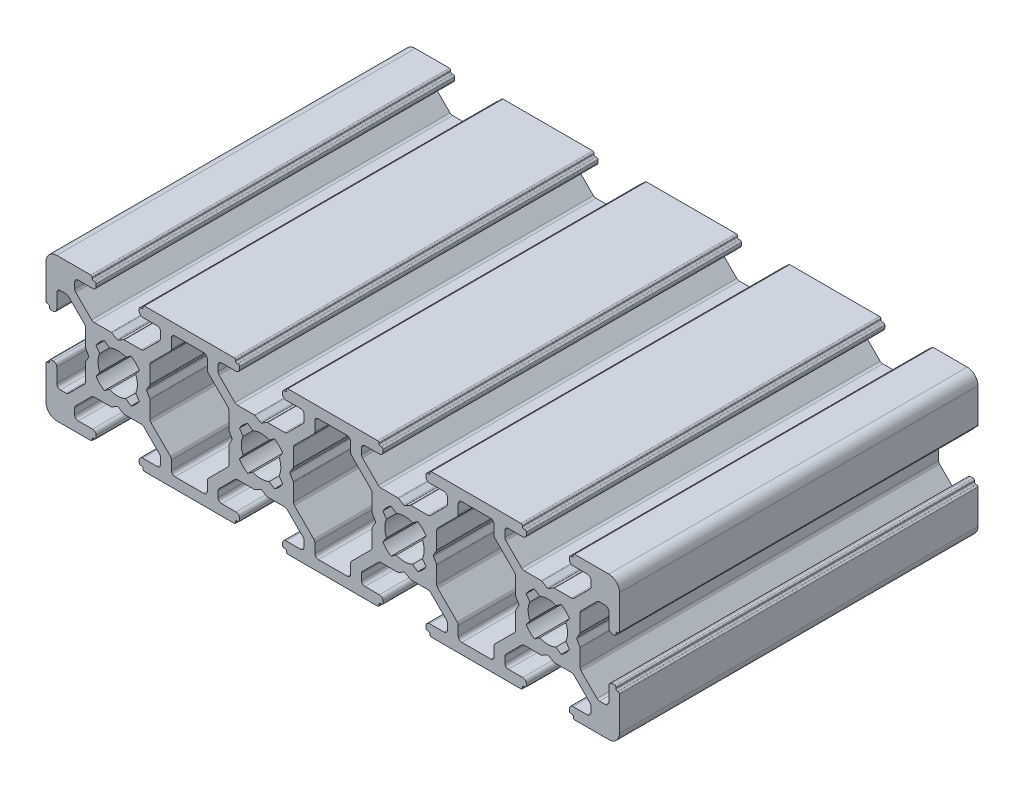
SolidWorks part; units mm, degrees
material "1060 СплавА"
ref_plane "Спереди" through (0, 0, 0) normal (0, 0, 1) x (1, 0, 0)
ref_plane "Сверху" through (0, 0, 0) normal (0, 1, 0) x (1, 0, 0)
ref_plane "Справа" through (0, 0, 0) normal (1, 0, 0) x (0, 0, -1)
sketch "Эскиз1" plane through (0, 0, 0) normal (0, 0, 1) x (1, 0, 0)
  line L0 (3.1454, -5.8536) -> (2.6464, -6.3525)
  line L1 (5.5, 0.9196) -> (5.5, 3.2919)
  line L2 (-13.6454, 4.6464) -> (-15.8536, 6.8546)
  line L3 (-18, 6) -> (-17.2081, 6)
  line L4 (-14.5, 0.9196) -> (-14.5, 3.2919)
  line L5 (-6.3546, -4.6464) -> (-4.1464, -6.8546)
  line L6 (-19.3, 3) -> (-19, 3)
  line L7 (-19.5, 3.35) -> (-19.5, 3.2)
  line L8 (-19.8, 3.55) -> (-19.7, 3.55)
  line L9 (-20, 8.5) -> (-20, 3.75)
  line L10 (-13.0204, 1.8653) -> (-12.5065, 1.1313)
  line L11 (-18.5, 3.5) -> (-18.5, 5.5)
  line L12 (-13.75, 10) -> (-18.5, 10)
  line L13 (-14.6464, 3.6454) -> (-16.8546, 5.8536)
  line L14 (-10.9196, 4.5) -> (-13.2919, 4.5)
  line L15 (-16, 8) -> (-16, 7.2081)
  line L16 (-14.0577, -0.1) -> (-14.4732, -0.8196)
  line L17 (-14.0577, 0.1) -> (-14.4732, 0.8196)
  line L18 (-11.8653, 3.0204) -> (-11.1313, 2.5065)
  line L19 (6.25, 10) -> (-6.25, 10)
  line L20 (-8.1347, 3.0204) -> (-8.8687, 2.5065)
  line L21 (-5.5, -0.9196) -> (-5.5, -3.2919)
  line L22 (-6.7081, 4.5) -> (-9.0804, 4.5)
  line L23 (-2.5, 8) -> (-2.5, 6.7061)
  line L24 (-3.1454, 5.8536) -> (-2.6464, 6.3525)
  line L25 (-10.1, 4.0577) -> (-10.8196, 4.4732)
  line L26 (-6.9796, 1.8653) -> (-7.4935, 1.1313)
  line L27 (-6.9796, -1.8653) -> (-7.4935, -1.1313)
  line L28 (-8.1347, -3.0204) -> (-8.8687, -2.5065)
  line L29 (-11.8653, -3.0204) -> (-11.1313, -2.5065)
  line L30 (-13.0204, -1.8653) -> (-12.5065, -1.1313)
  line L31 (-9.9, 4.0577) -> (-9.1804, 4.4732)
  line L32 (-13.5, 8.5) -> (-15.5, 8.5)
  line L33 (-13.55, 9.8) -> (-13.55, 9.7)
  line L34 (-13.35, 9.5) -> (-13.2, 9.5)
  line L35 (-13, 9.3) -> (-13, 9)
  line L36 (-10.9196, 4.5) -> (-13.2919, 4.5)
  line L37 (2, 8.5) -> (-2, 8.5)
  line L38 (-7, 9.3) -> (-7, 9)
  line L39 (-5.3536, 3.6454) -> (-3.1454, 5.8536)
  line L40 (-4, 8) -> (-4, 7.2081)
  line L41 (-6.3546, 4.6464) -> (-4.1464, 6.8546)
  line L42 (-6.65, 9.5) -> (-6.8, 9.5)
  line L43 (-6.45, 9.8) -> (-6.45, 9.7)
  line L44 (-6.5, 8.5) -> (-4.5, 8.5)
  line L45 (5.9423, -0.1) -> (5.5268, -0.8196)
  line L46 (-6.3546, -4.6464) -> (-4.1464, -6.8546)
  line L47 (-5.3536, -3.6454) -> (-3.1454, -5.8536)
  line L48 (-6.5, -8.5) -> (-4.5, -8.5)
  line L49 (-6.45, -9.8) -> (-6.45, -9.7)
  line L50 (-6.65, -9.5) -> (-6.8, -9.5)
  line L51 (-4, -8) -> (-4, -7.2081)
  line L52 (-5.3536, -3.6454) -> (-3.1454, -5.8536)
  line L53 (-7, -9.3) -> (-7, -9)
  line L54 (2, -8.5) -> (-2, -8.5)
  line L55 (-10.9196, -4.5) -> (-13.2919, -4.5)
  line L56 (-13, -9.3) -> (-13, -9)
  line L57 (-13.35, -9.5) -> (-13.2, -9.5)
  line L58 (-13.55, -9.8) -> (-13.55, -9.7)
  line L59 (-13.5, -8.5) -> (-15.5, -8.5)
  line L60 (-9.9, -4.0577) -> (-9.1804, -4.4732)
  line L61 (-13.0204, 1.8653) -> (-12.5065, 1.1313)
  line L62 (-11.8653, 3.0204) -> (-11.1313, 2.5065)
  line L63 (-8.1347, 3.0204) -> (-8.8687, 2.5065)
  line L64 (-6.9796, 1.8653) -> (-7.4935, 1.1313)
  line L65 (-6.9796, -1.8653) -> (-7.4935, -1.1313)
  line L66 (-10.1, -4.0577) -> (-10.8196, -4.4732)
  line L67 (-2.5, -8) -> (-2.5, -6.7061)
  line L68 (-6.7081, -4.5) -> (-9.0804, -4.5)
  line L69 (-5.9423, 0.1) -> (-5.5268, 0.8196)
  line L70 (-8.1347, -3.0204) -> (-8.8687, -2.5065)
  line L71 (-11.8653, -3.0204) -> (-11.1313, -2.5065)
  line L72 (-14.0577, -0.1) -> (-14.4732, -0.8196)
  line L73 (-14.0577, 0.1) -> (-14.4732, 0.8196)
  line L74 (-16, -8) -> (-16, -7.2081)
  line L75 (-10.9196, -4.5) -> (-13.2919, -4.5)
  line L76 (-14.6464, -3.6454) -> (-16.8546, -5.8536)
  line L77 (-13.75, -10) -> (-18.5, -10)
  line L78 (-18.5, -3.5) -> (-18.5, -5.5)
  line L79 (-13.0204, -1.8653) -> (-12.5065, -1.1313)
  line L80 (-20, -8.5) -> (-20, -3.75)
  line L81 (-19.8, -3.55) -> (-19.7, -3.55)
  line L82 (-19.5, -3.35) -> (-19.5, -3.2)
  line L83 (-19.3, -3) -> (-19, -3)
  line L84 (-14.5, -0.9196) -> (-14.5, -3.2919)
  line L85 (-18, -6) -> (-17.2081, -6)
  line L86 (-13.6454, -4.6464) -> (-15.8536, -6.8546)
  line L87 (6.25, -10) -> (-6.25, -10)
  line L88 (-5.3536, -3.6454) -> (-3.1454, -5.8536)
  line L89 (-5.9423, -0.1) -> (-5.5268, -0.8196)
  line L90 (-5.9423, 0.1) -> (-5.5268, 0.8196)
  line L91 (-5.9423, -0.1) -> (-5.5268, -0.8196)
  line L92 (-5.5, 0.9196) -> (-5.5, 3.2919)
  line L93 (-3.1454, -5.8536) -> (-2.6464, -6.3525)
  line L94 (5.9423, 0.1) -> (5.5268, 0.8196)
  line L95 (5.9423, -0.1) -> (5.5268, -0.8196)
  line L96 (5.3536, -3.6454) -> (3.1454, -5.8536)
  line L97 (13.6454, -4.6464) -> (15.8536, -6.8546)
  line L99 (14.5, -0.9196) -> (14.5, -3.2919)
  line L100 (13.75, 10) -> (26.25, 10)
  line L101 (13.75, -10) -> (26.25, -10)
  line L102 (13.6454, -4.6464) -> (15.8536, -6.8546)
  line L103 (14.5, -0.9196) -> (14.5, -3.2919)
  line L104 (13.0204, -1.8653) -> (12.5065, -1.1313)
  line L105 (17.5, 8) -> (17.5, 6.7061)
  line L106 (16.8546, 5.8536) -> (17.3536, 6.3525)
  line L107 (14.6464, -3.6454) -> (16.8546, -5.8536)
  line L108 (10.9196, -4.5) -> (13.2919, -4.5)
  line L109 (13.0204, 1.8653) -> (12.5065, 1.1313)
  line L110 (14.0577, 0.1) -> (14.4732, 0.8196)
  line L111 (14.0577, -0.1) -> (14.4732, -0.8196)
  line L112 (11.8653, -3.0204) -> (11.1313, -2.5065)
  line L113 (8.1347, -3.0204) -> (8.8687, -2.5065)
  line L114 (5.9423, 0.1) -> (5.5268, 0.8196)
  line L115 (6.7081, -4.5) -> (9.0804, -4.5)
  line L116 (2.5, -8) -> (2.5, -6.7061)
  line L117 (10.1, -4.0577) -> (10.8196, -4.4732)
  line L118 (6.9796, -1.8653) -> (7.4935, -1.1313)
  line L119 (6.9796, 1.8653) -> (7.4935, 1.1313)
  line L120 (8.1347, 3.0204) -> (8.8687, 2.5065)
  line L121 (11.8653, 3.0204) -> (11.1313, 2.5065)
  line L122 (13.0204, 1.8653) -> (12.5065, 1.1313)
  line L123 (9.9, -4.0577) -> (9.1804, -4.4732)
  line L124 (13.0204, -1.8653) -> (12.5065, -1.1313)
  line L125 (13, 9.3) -> (13, 9)
  line L126 (14.6464, 3.6454) -> (16.8546, 5.8536)
  line L127 (16, 8) -> (16, 7.2081)
  line L128 (10.9196, -4.5) -> (13.2919, -4.5)
  line L129 (7, -9.3) -> (7, -9)
  line L130 (5.3536, -3.6454) -> (3.1454, -5.8536)
  line L131 (4, -8) -> (4, -7.2081)
  line L132 (6.65, -9.5) -> (6.8, -9.5)
  line L133 (6.45, -9.8) -> (6.45, -9.7)
  line L134 (6.5, -8.5) -> (4.5, -8.5)
  line L135 (5.3536, -3.6454) -> (3.1454, -5.8536)
  line L136 (6.3546, -4.6464) -> (4.1464, -6.8546)
  line L137 (6.5, 8.5) -> (4.5, 8.5)
  line L138 (6.45, 9.8) -> (6.45, 9.7)
  line L139 (6.65, 9.5) -> (6.8, 9.5)
  line L140 (6.3546, 4.6464) -> (4.1464, 6.8546)
  line L141 (4, 8) -> (4, 7.2081)
  line L142 (5.3536, 3.6454) -> (3.1454, 5.8536)
  line L143 (7, 9.3) -> (7, 9)
  line L144 (10.9196, 4.5) -> (13.2919, 4.5)
  line L145 (13.6454, 4.6464) -> (15.8536, 6.8546)
  line L146 (13.35, 9.5) -> (13.2, 9.5)
  line L147 (13.55, 9.8) -> (13.55, 9.7)
  line L148 (13.5, 8.5) -> (15.5, 8.5)
  line L149 (9.9, 4.0577) -> (9.1804, 4.4732)
  line L150 (13.0204, -1.8653) -> (12.5065, -1.1313)
  line L151 (11.8653, -3.0204) -> (11.1313, -2.5065)
  line L152 (8.1347, -3.0204) -> (8.8687, -2.5065)
  line L153 (6.9796, -1.8653) -> (7.4935, -1.1313)
  line L154 (6.9796, 1.8653) -> (7.4935, 1.1313)
  line L155 (10.1, 4.0577) -> (10.8196, 4.4732)
  line L156 (3.1454, 5.8536) -> (2.6464, 6.3525)
  line L157 (2.5, 8) -> (2.5, 6.7061)
  line L158 (6.7081, 4.5) -> (9.0804, 4.5)
  line L159 (5.5, -0.9196) -> (5.5, -3.2919)
  line L160 (8.1347, 3.0204) -> (8.8687, 2.5065)
  line L161 (11.8653, 3.0204) -> (11.1313, 2.5065)
  line L162 (14.0577, 0.1) -> (14.4732, 0.8196)
  line L163 (14.0577, -0.1) -> (14.4732, -0.8196)
  line L164 (13.6454, -4.6464) -> (15.8536, -6.8546)
  line L165 (10.9196, 4.5) -> (13.2919, 4.5)
  line L166 (14.6464, 3.6454) -> (16.8546, 5.8536)
  line L167 (14.6464, -3.6454) -> (16.8546, -5.8536)
  line L168 (13.5, -8.5) -> (15.5, -8.5)
  line L169 (13.0204, 1.8653) -> (12.5065, 1.1313)
  line L170 (13.55, -9.8) -> (13.55, -9.7)
  line L171 (13.35, -9.5) -> (13.2, -9.5)
  line L172 (16, -8) -> (16, -7.2081)
  line L173 (14.6464, -3.6454) -> (16.8546, -5.8536)
  line L174 (6.3546, -4.6464) -> (4.1464, -6.8546)
  line L175 (14.5, 0.9196) -> (14.5, 3.2919)
  line L176 (13, -9.3) -> (13, -9)
  line L177 (13.6454, 4.6464) -> (15.8536, 6.8546)
  line L178 (13.0204, 1.8653) -> (12.5065, 1.1313)
  line L179 (13.0204, -1.8653) -> (12.5065, -1.1313)
  line L180 (17.5, -8) -> (17.5, -6.7061)
  line L181 (14.0577, 0.1) -> (14.4732, 0.8196)
  line L182 (14.6464, -3.6454) -> (16.8546, -5.8536)
  line L183 (14.0577, -0.1) -> (14.4732, -0.8196)
  line L184 (14.0577, 0.1) -> (14.4732, 0.8196)
  line L185 (18, -8.5) -> (22, -8.5)
  line L186 (14.0577, -0.1) -> (14.4732, -0.8196)
  line L187 (18, 8.5) -> (22, 8.5)
  line L188 (14.5, 0.9196) -> (14.5, 3.2919)
  line L189 (16.8546, -5.8536) -> (17.3536, -6.3525)
  line L190 (23.1454, -5.8536) -> (22.6464, -6.3525)
  line L191 (25.5, 0.9196) -> (25.5, 3.2919)
  line L192 (25.9423, -0.1) -> (25.5268, -0.8196)
  line L193 (25.9423, 0.1) -> (25.5268, 0.8196)
  line L194 (25.9423, -0.1) -> (25.5268, -0.8196)
  line L195 (25.3536, -3.6454) -> (23.1454, -5.8536)
  line L196 (25.9423, 0.1) -> (25.5268, 0.8196)
  line L197 (22.5, -8) -> (22.5, -6.7061)
  line L198 (26.9796, -1.8653) -> (27.4935, -1.1313)
  line L199 (26.9796, 1.8653) -> (27.4935, 1.1313)
  line L200 (26.3546, 4.6464) -> (24.1464, 6.8546)
  line L201 (27, -9.3) -> (27, -9)
  line L202 (25.5, 0.9196) -> (25.5, 3.2919)
  line L203 (33.6454, -4.6464) -> (35.8536, -6.8546)
  line L204 (25.3536, -3.6454) -> (23.1454, -5.8536)
  line L205 (24, -8) -> (24, -7.2081)
  line L206 (26.65, -9.5) -> (26.8, -9.5)
  line L207 (26.45, -9.8) -> (26.45, -9.7)
  line L208 (26.9796, 1.8653) -> (27.4935, 1.1313)
  line L209 (26.5, -8.5) -> (24.5, -8.5)
  line L210 (25.3536, -3.6454) -> (23.1454, -5.8536)
  line L211 (25.3536, 3.6454) -> (23.1454, 5.8536)
  line L212 (29.0804, 4.5) -> (26.7081, 4.5)
  line L213 (26.3546, -4.6464) -> (24.1464, -6.8546)
  line L214 (25.9423, -0.1) -> (25.5268, -0.8196)
  line L215 (25.9423, 0.1) -> (25.5268, 0.8196)
  line L216 (28.1347, 3.0204) -> (28.8687, 2.5065)
  line L217 (31.8653, 3.0204) -> (31.1313, 2.5065)
  line L218 (34.5, -0.9196) -> (34.5, -3.2919)
  line L219 (33.2919, 4.5) -> (30.9196, 4.5)
  line L220 (37.5, 8) -> (37.5, 6.7061)
  line L221 (36.8546, 5.8536) -> (37.3536, 6.3525)
  line L222 (29.9, 4.0577) -> (29.1804, 4.4732)
  line L223 (33.0204, 1.8653) -> (32.5065, 1.1313)
  line L224 (33.0204, -1.8653) -> (32.5065, -1.1313)
  line L225 (31.8653, -3.0204) -> (31.1313, -2.5065)
  line L226 (28.1347, -3.0204) -> (28.8687, -2.5065)
  line L227 (26.9796, -1.8653) -> (27.4935, -1.1313)
  line L228 (30.1, 4.0577) -> (30.8196, 4.4732)
  line L229 (26.5, 8.5) -> (24.5, 8.5)
  line L230 (26.45, 9.8) -> (26.45, 9.7)
  line L231 (26.65, 9.5) -> (26.8, 9.5)
  line L232 (26.3546, 4.6464) -> (24.1464, 6.8546)
  line L233 (29.0804, 4.5) -> (26.7081, 4.5)
  line L234 (33, 9.3) -> (33, 9)
  line L235 (34.6464, 3.6454) -> (36.8546, 5.8536)
  line L236 (36, 8) -> (36, 7.2081)
  line L237 (33.6454, 4.6464) -> (35.8536, 6.8546)
  line L238 (33.35, 9.5) -> (33.2, 9.5)
  line L239 (33.55, 9.8) -> (33.55, 9.7)
  line L240 (33.5, 8.5) -> (35.5, 8.5)
  line L241 (33.6454, -4.6464) -> (35.8536, -6.8546)
  line L242 (34.6464, -3.6454) -> (36.8546, -5.8536)
  line L243 (33.5, -8.5) -> (35.5, -8.5)
  line L244 (33.55, -9.8) -> (33.55, -9.7)
  line L245 (33.35, -9.5) -> (33.2, -9.5)
  line L246 (36, -8) -> (36, -7.2081)
  line L247 (34.6464, -3.6454) -> (36.8546, -5.8536)
  line L248 (33, -9.3) -> (33, -9)
  line L249 (29.0804, -4.5) -> (26.7081, -4.5)
  line L250 (24, 8) -> (24, 7.2081)
  line L251 (25.3536, 3.6454) -> (23.1454, 5.8536)
  line L252 (27, 9.3) -> (27, 9)
  line L253 (26.9796, -1.8653) -> (27.4935, -1.1313)
  line L254 (30.1, -4.0577) -> (30.8196, -4.4732)
  line L255 (26.9796, 1.8653) -> (27.4935, 1.1313)
  line L256 (28.1347, 3.0204) -> (28.8687, 2.5065)
  line L257 (31.8653, 3.0204) -> (31.1313, 2.5065)
  line L258 (33.0204, 1.8653) -> (32.5065, 1.1313)
  line L259 (33.0204, -1.8653) -> (32.5065, -1.1313)
  line L260 (29.9, -4.0577) -> (29.1804, -4.4732)
  line L261 (37.5, -8) -> (37.5, -6.7061)
  line L262 (33.2919, -4.5) -> (30.9196, -4.5)
  line L263 (34.0577, 0.1) -> (34.4732, 0.8196)
  line L264 (31.8653, -3.0204) -> (31.1313, -2.5065)
  line L265 (28.1347, -3.0204) -> (28.8687, -2.5065)
  line L266 (25.9423, -0.1) -> (25.5268, -0.8196)
  line L267 (25.9423, 0.1) -> (25.5268, 0.8196)
  line L268 (26.9796, 1.8653) -> (27.4935, 1.1313)
  line L269 (29.0804, -4.5) -> (26.7081, -4.5)
  line L270 (25.3536, -3.6454) -> (23.1454, -5.8536)
  line L271 (23.1454, 5.8536) -> (22.6464, 6.3525)
  line L272 (22.5, 8) -> (22.5, 6.7061)
  line L273 (26.9796, -1.8653) -> (27.4935, -1.1313)
  line L274 (25.5, -0.9196) -> (25.5, -3.2919)
  line L275 (26.3546, -4.6464) -> (24.1464, -6.8546)
  line L276 (25.5, -0.9196) -> (25.5, -3.2919)
  line L277 (26.3546, -4.6464) -> (24.1464, -6.8546)
  line L278 (34.6464, -3.6454) -> (36.8546, -5.8536)
  line L279 (34.0577, -0.1) -> (34.4732, -0.8196)
  line L280 (34.0577, 0.1) -> (34.4732, 0.8196)
  line L281 (43.1454, -5.8536) -> (42.6464, -6.3525)
  line L282 (45.5, 0.9196) -> (45.5, 3.2919)
  line L283 (45.9423, -0.1) -> (45.5268, -0.8196)
  line L284 (45.9423, 0.1) -> (45.5268, 0.8196)
  line L285 (45.9423, -0.1) -> (45.5268, -0.8196)
  line L286 (45.3536, -3.6454) -> (43.1454, -5.8536)
  line L287 (33.75, -10) -> (46.25, -10)
  line L288 (53.6454, -4.6464) -> (55.8536, -6.8546)
  line L289 (58, -6) -> (57.2081, -6)
  line L290 (54.5, -0.9196) -> (54.5, -3.2919)
  line L291 (59.3, -3) -> (59, -3)
  line L292 (59.5, -3.35) -> (59.5, -3.2)
  line L293 (59.8, -3.55) -> (59.7, -3.55)
  line L294 (60, -8.5) -> (60, -3.75)
  line L295 (53.0204, -1.8653) -> (52.5065, -1.1313)
  line L296 (58.5, -3.5) -> (58.5, -5.5)
  line L297 (53.75, -10) -> (58.5, -10)
  line L298 (54.6464, -3.6454) -> (56.8546, -5.8536)
  line L299 (50.9196, -4.5) -> (53.2919, -4.5)
  line L300 (56, -8) -> (56, -7.2081)
  line L301 (54.0577, 0.1) -> (54.4732, 0.8196)
  line L302 (54.0577, -0.1) -> (54.4732, -0.8196)
  line L303 (51.8653, -3.0204) -> (51.1313, -2.5065)
  line L304 (48.1347, -3.0204) -> (48.8687, -2.5065)
  line L305 (45.9423, 0.1) -> (45.5268, 0.8196)
  line L306 (46.7081, -4.5) -> (49.0804, -4.5)
  line L307 (42.5, -8) -> (42.5, -6.7061)
  line L308 (50.1, -4.0577) -> (50.8196, -4.4732)
  line L309 (46.9796, -1.8653) -> (47.4935, -1.1313)
  line L310 (46.9796, 1.8653) -> (47.4935, 1.1313)
  line L311 (48.1347, 3.0204) -> (48.8687, 2.5065)
  line L312 (51.8653, 3.0204) -> (51.1313, 2.5065)
  line L313 (53.0204, 1.8653) -> (52.5065, 1.1313)
  line L314 (49.9, -4.0577) -> (49.1804, -4.4732)
  line L315 (53.5, -8.5) -> (55.5, -8.5)
  line L316 (53.55, -9.8) -> (53.55, -9.7)
  line L317 (53.35, -9.5) -> (53.2, -9.5)
  line L318 (53, -9.3) -> (53, -9)
  line L319 (50.9196, -4.5) -> (53.2919, -4.5)
  line L320 (38, -8.5) -> (42, -8.5)
  line L321 (47, -9.3) -> (47, -9)
  line L322 (45.3536, -3.6454) -> (43.1454, -5.8536)
  line L323 (44, -8) -> (44, -7.2081)
  line L324 (46.65, -9.5) -> (46.8, -9.5)
  line L325 (46.45, -9.8) -> (46.45, -9.7)
  line L326 (46.5, -8.5) -> (44.5, -8.5)
  line L327 (45.3536, -3.6454) -> (43.1454, -5.8536)
  line L328 (46.3546, -4.6464) -> (44.1464, -6.8546)
  line L329 (34.0577, -0.1) -> (34.4732, -0.8196)
  line L330 (46.5, 8.5) -> (44.5, 8.5)
  line L331 (46.45, 9.8) -> (46.45, 9.7)
  line L332 (46.65, 9.5) -> (46.8, 9.5)
  line L333 (46.3546, 4.6464) -> (44.1464, 6.8546)
  line L334 (44, 8) -> (44, 7.2081)
  line L335 (45.3536, 3.6454) -> (43.1454, 5.8536)
  line L336 (47, 9.3) -> (47, 9)
  line L337 (38, 8.5) -> (42, 8.5)
  line L338 (50.9196, 4.5) -> (53.2919, 4.5)
  line L339 (53, 9.3) -> (53, 9)
  line L340 (53.35, 9.5) -> (53.2, 9.5)
  line L341 (53.55, 9.8) -> (53.55, 9.7)
  line L342 (53.5, 8.5) -> (55.5, 8.5)
  line L343 (49.9, 4.0577) -> (49.1804, 4.4732)
  line L344 (53.0204, -1.8653) -> (52.5065, -1.1313)
  line L345 (51.8653, -3.0204) -> (51.1313, -2.5065)
  line L346 (48.1347, -3.0204) -> (48.8687, -2.5065)
  line L347 (46.9796, -1.8653) -> (47.4935, -1.1313)
  line L348 (46.9796, 1.8653) -> (47.4935, 1.1313)
  line L349 (50.1, 4.0577) -> (50.8196, 4.4732)
  line L350 (43.1454, 5.8536) -> (42.6464, 6.3525)
  line L351 (42.5, 8) -> (42.5, 6.7061)
  line L352 (46.7081, 4.5) -> (49.0804, 4.5)
  line L353 (45.5, -0.9196) -> (45.5, -3.2919)
  line L354 (48.1347, 3.0204) -> (48.8687, 2.5065)
  line L355 (33.75, 10) -> (46.25, 10)
  line L356 (51.8653, 3.0204) -> (51.1313, 2.5065)
  line L357 (54.0577, 0.1) -> (54.4732, 0.8196)
  line L358 (54.0577, -0.1) -> (54.4732, -0.8196)
  line L359 (56, 8) -> (56, 7.2081)
  line L360 (50.9196, 4.5) -> (53.2919, 4.5)
  line L361 (54.6464, 3.6454) -> (56.8546, 5.8536)
  line L362 (53.75, 10) -> (58.5, 10)
  line L363 (58.5, 3.5) -> (58.5, 5.5)
  line L364 (53.0204, 1.8653) -> (52.5065, 1.1313)
  line L365 (60, 8.5) -> (60, 3.75)
  line L366 (59.8, 3.55) -> (59.7, 3.55)
  line L367 (59.5, 3.35) -> (59.5, 3.2)
  line L368 (59.3, 3) -> (59, 3)
  line L369 (46.3546, -4.6464) -> (44.1464, -6.8546)
  line L370 (54.5, 0.9196) -> (54.5, 3.2919)
  line L371 (58, 6) -> (57.2081, 6)
  line L372 (53.6454, 4.6464) -> (55.8536, 6.8546)
  line L373 (34.5, 0.9196) -> (34.5, 3.2919)
  line L374 (36.8546, -5.8536) -> (37.3536, -6.3525)
  arc A0 (-17.2081, 6) -> (-16.8546, 5.8536) centre (-17.2081, 5.5) cw
  arc A1 (-14.5, 3.2919) -> (-14.6464, 3.6454) centre (-15, 3.2919) ccw
  arc A2 (-16, 7.2081) -> (-15.8536, 6.8546) centre (-15.5, 7.2081) ccw
  arc A3 (-18.5, 10) -> (-20, 8.5) centre (-18.5, 8.5) ccw
  arc A4 (-19.7, 3.55) -> (-19.5, 3.35) centre (-19.7, 3.35) cw
  arc A5 (-20, 3.75) -> (-19.8, 3.55) centre (-19.8, 3.75) ccw
  arc A6 (-19.5, 3.2) -> (-19.3, 3) centre (-19.3, 3.2) ccw
  arc A7 (-19, 3) -> (-18.5, 3.5) centre (-19, 3.5) ccw
  arc A8 (-18, 6) -> (-18.5, 5.5) centre (-18, 5.5) ccw
  arc A9 (-13.2919, 4.5) -> (-13.6454, 4.6464) centre (-13.2919, 5) cw
  arc A10 (-14.4732, -0.8196) -> (-14.5, -0.9196) centre (-14.3, -0.9196) ccw
  arc A11 (-14.4732, 0.8196) -> (-14.5, 0.9196) centre (-14.3, 0.9196) cw
  arc A12 (-14.0577, 0.1) -> (-14.0577, -0.1) centre (-14.2309, 0) cw
  arc A13 (-10.1, 4.0577) -> (-9.9, 4.0577) centre (-10, 4.2309) ccw
  arc A14 (-13.0204, -1.8653) -> (-11.8653, -3.0204) centre (-10, 0) ccw
  arc A15 (-12.5065, 1.1313) -> (-12.5065, -1.1313) centre (-10, 0) ccw
  arc A16 (-8.8687, 2.5065) -> (-11.1313, 2.5065) centre (-10, 0) ccw
  arc A17 (-7.4935, -1.1313) -> (-7.4935, 1.1313) centre (-10, 0) ccw
  arc A18 (-11.1313, -2.5065) -> (-8.8687, -2.5065) centre (-10, 0) ccw
  arc A19 (-11.8653, 3.0204) -> (-13.0204, 1.8653) centre (-10, 0) ccw
  arc A20 (-6.9796, 1.8653) -> (-8.1347, 3.0204) centre (-10, 0) ccw
  arc A21 (-8.1347, -3.0204) -> (-6.9796, -1.8653) centre (-10, 0) ccw
  arc A22 (-10.8196, 4.4732) -> (-10.9196, 4.5) centre (-10.9196, 4.3) ccw
  arc A23 (-9.1804, 4.4732) -> (-9.0804, 4.5) centre (-9.0804, 4.3) cw
  arc A24 (-16, 8) -> (-15.5, 8.5) centre (-15.5, 8) cw
  arc A25 (-13, 9) -> (-13.5, 8.5) centre (-13.5, 9) cw
  arc A26 (-13.2, 9.5) -> (-13, 9.3) centre (-13.2, 9.3) cw
  arc A27 (-13.75, 10) -> (-13.55, 9.8) centre (-13.75, 9.8) cw
  arc A28 (-13.55, 9.7) -> (-13.35, 9.5) centre (-13.35, 9.7) ccw
  arc A29 (-6.45, 9.7) -> (-6.65, 9.5) centre (-6.65, 9.7) cw
  arc A30 (-6.25, 10) -> (-6.45, 9.8) centre (-6.25, 9.8) ccw
  arc A31 (-6.8, 9.5) -> (-7, 9.3) centre (-6.8, 9.3) ccw
  arc A32 (-7, 9) -> (-6.5, 8.5) centre (-6.5, 9) ccw
  arc A33 (-2, 8.5) -> (-2.5, 8) centre (-2, 8) ccw
  arc A34 (-6.7081, 4.5) -> (-6.3546, 4.6464) centre (-6.7081, 5) ccw
  arc A35 (-2.6464, 6.3525) -> (-2.5, 6.7061) centre (-3, 6.7061) ccw
  arc A36 (-4.1464, 6.8546) -> (-4, 7.2081) centre (-4.5, 7.2081) ccw
  arc A37 (-4.5, 8.5) -> (-4, 8) centre (-4.5, 8) cw
  arc A38 (-5.5, -3.2919) -> (-5.3536, -3.6454) centre (-5, -3.2919) ccw
  arc A39 (-4.5, -8.5) -> (-4, -8) centre (-4.5, -8) ccw
  arc A40 (-4.1464, -6.8546) -> (-4, -7.2081) centre (-4.5, -7.2081) cw
  arc A41 (-2, -8.5) -> (-2.5, -8) centre (-2, -8) cw
  arc A42 (-5.5, 3.2919) -> (-5.3536, 3.6454) centre (-5, 3.2919) cw
  arc A43 (-7, -9) -> (-6.5, -8.5) centre (-6.5, -9) cw
  arc A44 (-6.8, -9.5) -> (-7, -9.3) centre (-6.8, -9.3) cw
  arc A45 (-5.5, -3.2919) -> (-5.3536, -3.6454) centre (-5, -3.2919) ccw
  arc A46 (-6.25, -10) -> (-6.45, -9.8) centre (-6.25, -9.8) cw
  arc A47 (-6.45, -9.7) -> (-6.65, -9.5) centre (-6.65, -9.7) ccw
  arc A48 (-2.6464, -6.3525) -> (-2.5, -6.7061) centre (-3, -6.7061) cw
  arc A49 (5.5268, -0.8196) -> (5.5, -0.9196) centre (5.7, -0.9196) ccw
  arc A50 (5.5268, 0.8196) -> (5.5, 0.9196) centre (5.7, 0.9196) cw
  arc A51 (5.9423, 0.1) -> (5.9423, -0.1) centre (5.7691, 0) cw
  arc A52 (5.5268, -0.8196) -> (5.5, -0.9196) centre (5.7, -0.9196) ccw
  arc A53 (-6.7081, -4.5) -> (-6.3546, -4.6464) centre (-6.7081, -5) cw
  arc A54 (5.5268, 0.8196) -> (5.5, 0.9196) centre (5.7, 0.9196) cw
  arc A55 (12.5065, -1.1313) -> (12.5065, 1.1313) centre (10, 0) ccw
  arc A56 (14.5, -3.2919) -> (14.6464, -3.6454) centre (15, -3.2919) ccw
  arc A57 (13.0204, 1.8653) -> (11.8653, 3.0204) centre (10, 0) ccw
  arc A58 (11.8653, -3.0204) -> (13.0204, -1.8653) centre (10, 0) ccw
  arc A59 (-13.55, -9.7) -> (-13.35, -9.5) centre (-13.35, -9.7) cw
  arc A60 (-13.75, -10) -> (-13.55, -9.8) centre (-13.75, -9.8) ccw
  arc A61 (-13.2, -9.5) -> (-13, -9.3) centre (-13.2, -9.3) ccw
  arc A62 (-13, -9) -> (-13.5, -8.5) centre (-13.5, -9) ccw
  arc A63 (-16, -8) -> (-15.5, -8.5) centre (-15.5, -8) ccw
  arc A64 (-9.1804, -4.4732) -> (-9.0804, -4.5) centre (-9.0804, -4.3) ccw
  arc A65 (-10.8196, -4.4732) -> (-10.9196, -4.5) centre (-10.9196, -4.3) cw
  arc A66 (-8.1347, 3.0204) -> (-6.9796, 1.8653) centre (-10, 0) cw
  arc A67 (-6.9796, -1.8653) -> (-8.1347, -3.0204) centre (-10, 0) cw
  arc A68 (-11.8653, -3.0204) -> (-13.0204, -1.8653) centre (-10, 0) cw
  arc A69 (-11.1313, 2.5065) -> (-8.8687, 2.5065) centre (-10, 0) cw
  arc A70 (-8.8687, -2.5065) -> (-11.1313, -2.5065) centre (-10, 0) cw
  arc A71 (-13.0204, 1.8653) -> (-11.8653, 3.0204) centre (-10, 0) cw
  arc A72 (-10.1, -4.0577) -> (-9.9, -4.0577) centre (-10, -4.2309) cw
  arc A73 (-14.4732, -0.8196) -> (-14.5, -0.9196) centre (-14.3, -0.9196) ccw
  arc A74 (-14.4732, 0.8196) -> (-14.5, 0.9196) centre (-14.3, 0.9196) cw
  arc A75 (-13.2919, -4.5) -> (-13.6454, -4.6464) centre (-13.2919, -5) ccw
  arc A76 (-18, -6) -> (-18.5, -5.5) centre (-18, -5.5) cw
  arc A77 (-19, -3) -> (-18.5, -3.5) centre (-19, -3.5) cw
  arc A78 (-19.5, -3.2) -> (-19.3, -3) centre (-19.3, -3.2) cw
  arc A79 (-20, -3.75) -> (-19.8, -3.55) centre (-19.8, -3.75) cw
  arc A80 (-19.7, -3.55) -> (-19.5, -3.35) centre (-19.7, -3.35) ccw
  arc A81 (-18.5, -10) -> (-20, -8.5) centre (-18.5, -8.5) cw
  arc A82 (-16, -7.2081) -> (-15.8536, -6.8546) centre (-15.5, -7.2081) cw
  arc A83 (-14.5, -3.2919) -> (-14.6464, -3.6454) centre (-15, -3.2919) cw
  arc A84 (-17.2081, -6) -> (-16.8546, -5.8536) centre (-17.2081, -5.5) ccw
  arc A85 (-5.5268, 0.8196) -> (-5.5, 0.9196) centre (-5.7, 0.9196) ccw
  arc A86 (-5.5268, -0.8196) -> (-5.5, -0.9196) centre (-5.7, -0.9196) cw
  arc A87 (-5.9423, 0.1) -> (-5.9423, -0.1) centre (-5.7691, 0) ccw
  arc A88 (-5.5268, 0.8196) -> (-5.5, 0.9196) centre (-5.7, 0.9196) ccw
  arc A89 (-5.5268, -0.8196) -> (-5.5, -0.9196) centre (-5.7, -0.9196) cw
  arc A90 (13.55, 9.7) -> (13.35, 9.5) centre (13.35, 9.7) cw
  arc A91 (13.75, 10) -> (13.55, 9.8) centre (13.75, 9.8) ccw
  arc A92 (13.2, 9.5) -> (13, 9.3) centre (13.2, 9.3) ccw
  arc A93 (13, 9) -> (13.5, 8.5) centre (13.5, 9) ccw
  arc A94 (18, 8.5) -> (17.5, 8) centre (18, 8) ccw
  arc A95 (13.2919, -4.5) -> (13.6454, -4.6464) centre (13.2919, -5) cw
  arc A96 (14.4732, 0.8196) -> (14.5, 0.9196) centre (14.3, 0.9196) ccw
  arc A97 (14.4732, -0.8196) -> (14.5, -0.9196) centre (14.3, -0.9196) cw
  arc A98 (10.1, -4.0577) -> (9.9, -4.0577) centre (10, -4.2309) ccw
  arc A99 (13.0204, 1.8653) -> (11.8653, 3.0204) centre (10, 0) ccw
  arc A100 (8.8687, -2.5065) -> (11.1313, -2.5065) centre (10, 0) ccw
  arc A101 (11.1313, 2.5065) -> (8.8687, 2.5065) centre (10, 0) ccw
  arc A102 (11.8653, -3.0204) -> (13.0204, -1.8653) centre (10, 0) ccw
  arc A103 (6.9796, -1.8653) -> (8.1347, -3.0204) centre (10, 0) ccw
  arc A104 (8.1347, 3.0204) -> (6.9796, 1.8653) centre (10, 0) ccw
  arc A105 (10.8196, -4.4732) -> (10.9196, -4.5) centre (10.9196, -4.3) ccw
  arc A106 (9.1804, -4.4732) -> (9.0804, -4.5) centre (9.0804, -4.3) cw
  arc A107 (13.2919, 4.5) -> (13.6454, 4.6464) centre (13.2919, 5) ccw
  arc A108 (17.3536, 6.3525) -> (17.5, 6.7061) centre (17, 6.7061) ccw
  arc A109 (15.8536, 6.8546) -> (16, 7.2081) centre (15.5, 7.2081) ccw
  arc A110 (15.5, 8.5) -> (16, 8) centre (15.5, 8) cw
  arc A111 (14.5, -3.2919) -> (14.6464, -3.6454) centre (15, -3.2919) ccw
  arc A112 (6.7081, -4.5) -> (6.3546, -4.6464) centre (6.7081, -5) ccw
  arc A113 (2.6464, -6.3525) -> (2.5, -6.7061) centre (3, -6.7061) ccw
  arc A114 (6.45, -9.7) -> (6.65, -9.5) centre (6.65, -9.7) cw
  arc A115 (6.25, -10) -> (6.45, -9.8) centre (6.25, -9.8) ccw
  arc A116 (5.5, -3.2919) -> (5.3536, -3.6454) centre (5, -3.2919) cw
  arc A117 (6.8, -9.5) -> (7, -9.3) centre (6.8, -9.3) ccw
  arc A118 (7, -9) -> (6.5, -8.5) centre (6.5, -9) ccw
  arc A119 (5.5, 3.2919) -> (5.3536, 3.6454) centre (5, 3.2919) ccw
  arc A120 (2, -8.5) -> (2.5, -8) centre (2, -8) ccw
  arc A121 (4.1464, -6.8546) -> (4, -7.2081) centre (4.5, -7.2081) ccw
  arc A122 (4.5, -8.5) -> (4, -8) centre (4.5, -8) cw
  arc A123 (5.5, -3.2919) -> (5.3536, -3.6454) centre (5, -3.2919) cw
  arc A124 (4.5, 8.5) -> (4, 8) centre (4.5, 8) ccw
  arc A125 (4.1464, 6.8546) -> (4, 7.2081) centre (4.5, 7.2081) cw
  arc A126 (2.6464, 6.3525) -> (2.5, 6.7061) centre (3, 6.7061) cw
  arc A127 (6.7081, 4.5) -> (6.3546, 4.6464) centre (6.7081, 5) cw
  arc A128 (2, 8.5) -> (2.5, 8) centre (2, 8) cw
  arc A129 (7, 9) -> (6.5, 8.5) centre (6.5, 9) cw
  arc A130 (6.8, 9.5) -> (7, 9.3) centre (6.8, 9.3) cw
  arc A131 (6.25, 10) -> (6.45, 9.8) centre (6.25, 9.8) cw
  arc A132 (6.45, 9.7) -> (6.65, 9.5) centre (6.65, 9.7) ccw
  arc A133 (15.5, -8.5) -> (16, -8) centre (15.5, -8) ccw
  arc A134 (15.8536, -6.8546) -> (16, -7.2081) centre (15.5, -7.2081) cw
  arc A135 (18, -8.5) -> (17.5, -8) centre (18, -8) cw
  arc A136 (14.5, 3.2919) -> (14.6464, 3.6454) centre (15, 3.2919) cw
  arc A137 (13, -9) -> (13.5, -8.5) centre (13.5, -9) cw
  arc A138 (9.1804, 4.4732) -> (9.0804, 4.5) centre (9.0804, 4.3) ccw
  arc A139 (10.8196, 4.4732) -> (10.9196, 4.5) centre (10.9196, 4.3) cw
  arc A140 (8.1347, -3.0204) -> (6.9796, -1.8653) centre (10, 0) cw
  arc A141 (6.9796, 1.8653) -> (8.1347, 3.0204) centre (10, 0) cw
  arc A142 (11.8653, 3.0204) -> (13.0204, 1.8653) centre (10, 0) cw
  arc A143 (11.1313, -2.5065) -> (8.8687, -2.5065) centre (10, 0) cw
  arc A144 (7.4935, -1.1313) -> (7.4935, 1.1313) centre (10, 0) cw
  arc A145 (8.8687, 2.5065) -> (11.1313, 2.5065) centre (10, 0) cw
  arc A146 (12.5065, 1.1313) -> (12.5065, -1.1313) centre (10, 0) cw
  arc A147 (13.0204, -1.8653) -> (11.8653, -3.0204) centre (10, 0) cw
  arc A148 (10.1, 4.0577) -> (9.9, 4.0577) centre (10, 4.2309) cw
  arc A149 (14.0577, 0.1) -> (14.0577, -0.1) centre (14.2309, 0) ccw
  arc A150 (14.4732, 0.8196) -> (14.5, 0.9196) centre (14.3, 0.9196) ccw
  arc A151 (14.4732, -0.8196) -> (14.5, -0.9196) centre (14.3, -0.9196) cw
  arc A152 (13.2919, 4.5) -> (13.6454, 4.6464) centre (13.2919, 5) ccw
  arc A153 (13.2, -9.5) -> (13, -9.3) centre (13.2, -9.3) cw
  arc A154 (14.5, -3.2919) -> (14.6464, -3.6454) centre (15, -3.2919) ccw
  arc A155 (13.75, -10) -> (13.55, -9.8) centre (13.75, -9.8) cw
  arc A156 (13.55, -9.7) -> (13.35, -9.5) centre (13.35, -9.7) ccw
  arc A157 (17.3536, -6.3525) -> (17.5, -6.7061) centre (17, -6.7061) cw
  arc A158 (13.2919, -4.5) -> (13.6454, -4.6464) centre (13.2919, -5) cw
  arc A159 (11.8653, 3.0204) -> (13.0204, 1.8653) centre (10, 0) cw
  arc A160 (14.5, 3.2919) -> (14.6464, 3.6454) centre (15, 3.2919) cw
  arc A161 (13.0204, -1.8653) -> (11.8653, -3.0204) centre (10, 0) cw
  arc A162 (14.4732, 0.8196) -> (14.5, 0.9196) centre (14.3, 0.9196) ccw
  arc A163 (14.4732, -0.8196) -> (14.5, -0.9196) centre (14.3, -0.9196) cw
  arc A164 (14.0577, 0.1) -> (14.0577, -0.1) centre (14.2309, 0) ccw
  arc A165 (14.4732, 0.8196) -> (14.5, 0.9196) centre (14.3, 0.9196) ccw
  arc A166 (14.4732, -0.8196) -> (14.5, -0.9196) centre (14.3, -0.9196) cw
  arc A167 (25.5268, -0.8196) -> (25.5, -0.9196) centre (25.7, -0.9196) ccw
  arc A168 (25.5268, 0.8196) -> (25.5, 0.9196) centre (25.7, 0.9196) cw
  arc A169 (25.9423, 0.1) -> (25.9423, -0.1) centre (25.7691, 0) cw
  arc A170 (25.5268, -0.8196) -> (25.5, -0.9196) centre (25.7, -0.9196) ccw
  arc A171 (25.5268, 0.8196) -> (25.5, 0.9196) centre (25.7, 0.9196) cw
  arc A172 (26.9796, -1.8653) -> (28.1347, -3.0204) centre (30, 0) ccw
  arc A173 (25.5, 3.2919) -> (25.3536, 3.6454) centre (25, 3.2919) ccw
  arc A174 (28.1347, 3.0204) -> (26.9796, 1.8653) centre (30, 0) ccw
  arc A175 (26.7081, -4.5) -> (26.3546, -4.6464) centre (26.7081, -5) ccw
  arc A176 (22.6464, -6.3525) -> (22.5, -6.7061) centre (23, -6.7061) ccw
  arc A177 (26.45, -9.7) -> (26.65, -9.5) centre (26.65, -9.7) cw
  arc A178 (26.25, -10) -> (26.45, -9.8) centre (26.25, -9.8) ccw
  arc A179 (25.5, -3.2919) -> (25.3536, -3.6454) centre (25, -3.2919) cw
  arc A180 (26.8, -9.5) -> (27, -9.3) centre (26.8, -9.3) ccw
  arc A181 (26.7081, 4.5) -> (26.3546, 4.6464) centre (26.7081, 5) cw
  arc A182 (25.5268, -0.8196) -> (25.5, -0.9196) centre (25.7, -0.9196) ccw
  arc A183 (25.5268, 0.8196) -> (25.5, 0.9196) centre (25.7, 0.9196) cw
  arc A184 (25.9423, 0.1) -> (25.9423, -0.1) centre (25.7691, 0) cw
  arc A185 (29.9, 4.0577) -> (30.1, 4.0577) centre (30, 4.2309) ccw
  arc A186 (26.9796, -1.8653) -> (28.1347, -3.0204) centre (30, 0) ccw
  arc A187 (27.4935, 1.1313) -> (27.4935, -1.1313) centre (30, 0) ccw
  arc A188 (31.1313, 2.5065) -> (28.8687, 2.5065) centre (30, 0) ccw
  arc A189 (32.5065, -1.1313) -> (32.5065, 1.1313) centre (30, 0) ccw
  arc A190 (28.8687, -2.5065) -> (31.1313, -2.5065) centre (30, 0) ccw
  arc A191 (28.1347, 3.0204) -> (26.9796, 1.8653) centre (30, 0) ccw
  arc A192 (33.0204, 1.8653) -> (31.8653, 3.0204) centre (30, 0) ccw
  arc A193 (31.8653, -3.0204) -> (33.0204, -1.8653) centre (30, 0) ccw
  arc A194 (29.1804, 4.4732) -> (29.0804, 4.5) centre (29.0804, 4.3) ccw
  arc A195 (30.8196, 4.4732) -> (30.9196, 4.5) centre (30.9196, 4.3) cw
  arc A196 (27, -9) -> (26.5, -8.5) centre (26.5, -9) ccw
  arc A197 (25.5, 3.2919) -> (25.3536, 3.6454) centre (25, 3.2919) ccw
  arc A198 (22, -8.5) -> (22.5, -8) centre (22, -8) ccw
  arc A199 (24.1464, -6.8546) -> (24, -7.2081) centre (24.5, -7.2081) ccw
  arc A200 (24.5, -8.5) -> (24, -8) centre (24.5, -8) cw
  arc A201 (33.55, 9.7) -> (33.35, 9.5) centre (33.35, 9.7) cw
  arc A202 (33.75, 10) -> (33.55, 9.8) centre (33.75, 9.8) ccw
  arc A203 (33.2, 9.5) -> (33, 9.3) centre (33.2, 9.3) ccw
  arc A204 (33, 9) -> (33.5, 8.5) centre (33.5, 9) ccw
  arc A205 (38, 8.5) -> (37.5, 8) centre (38, 8) ccw
  arc A206 (33.2919, 4.5) -> (33.6454, 4.6464) centre (33.2919, 5) ccw
  arc A207 (37.3536, 6.3525) -> (37.5, 6.7061) centre (37, 6.7061) ccw
  arc A208 (35.8536, 6.8546) -> (36, 7.2081) centre (35.5, 7.2081) ccw
  arc A209 (35.5, 8.5) -> (36, 8) centre (35.5, 8) cw
  arc A210 (34.5, -3.2919) -> (34.6464, -3.6454) centre (35, -3.2919) ccw
  arc A211 (35.5, -8.5) -> (36, -8) centre (35.5, -8) ccw
  arc A212 (35.8536, -6.8546) -> (36, -7.2081) centre (35.5, -7.2081) cw
  arc A213 (38, -8.5) -> (37.5, -8) centre (38, -8) cw
  arc A214 (34.5, 3.2919) -> (34.6464, 3.6454) centre (35, 3.2919) cw
  arc A215 (33, -9) -> (33.5, -8.5) centre (33.5, -9) cw
  arc A216 (33.2, -9.5) -> (33, -9.3) centre (33.2, -9.3) cw
  arc A217 (34.5, -3.2919) -> (34.6464, -3.6454) centre (35, -3.2919) ccw
  arc A218 (33.75, -10) -> (33.55, -9.8) centre (33.75, -9.8) cw
  arc A219 (33.55, -9.7) -> (33.35, -9.5) centre (33.35, -9.7) ccw
  arc A220 (37.3536, -6.3525) -> (37.5, -6.7061) centre (37, -6.7061) cw
  arc A221 (33.2919, -4.5) -> (33.6454, -4.6464) centre (33.2919, -5) cw
  arc A222 (25.5, -3.2919) -> (25.3536, -3.6454) centre (25, -3.2919) cw
  arc A223 (24.5, 8.5) -> (24, 8) centre (24.5, 8) ccw
  arc A224 (24.1464, 6.8546) -> (24, 7.2081) centre (24.5, 7.2081) cw
  arc A225 (22.6464, 6.3525) -> (22.5, 6.7061) centre (23, 6.7061) cw
  arc A226 (26.7081, 4.5) -> (26.3546, 4.6464) centre (26.7081, 5) cw
  arc A227 (30.8196, -4.4732) -> (30.9196, -4.5) centre (30.9196, -4.3) ccw
  arc A228 (29.1804, -4.4732) -> (29.0804, -4.5) centre (29.0804, -4.3) cw
  arc A229 (31.8653, 3.0204) -> (33.0204, 1.8653) centre (30, 0) cw
  arc A230 (33.0204, -1.8653) -> (31.8653, -3.0204) centre (30, 0) cw
  arc A231 (28.1347, -3.0204) -> (26.9796, -1.8653) centre (30, 0) cw
  arc A232 (28.8687, 2.5065) -> (31.1313, 2.5065) centre (30, 0) cw
  arc A233 (31.1313, -2.5065) -> (28.8687, -2.5065) centre (30, 0) cw
  arc A234 (26.9796, 1.8653) -> (28.1347, 3.0204) centre (30, 0) cw
  arc A235 (29.9, -4.0577) -> (30.1, -4.0577) centre (30, -4.2309) cw
  arc A236 (25.5268, -0.8196) -> (25.5, -0.9196) centre (25.7, -0.9196) ccw
  arc A237 (25.5268, 0.8196) -> (25.5, 0.9196) centre (25.7, 0.9196) cw
  arc A238 (26.7081, -4.5) -> (26.3546, -4.6464) centre (26.7081, -5) ccw
  arc A239 (22, 8.5) -> (22.5, 8) centre (22, 8) cw
  arc A240 (27, 9) -> (26.5, 8.5) centre (26.5, 9) cw
  arc A241 (26.8, 9.5) -> (27, 9.3) centre (26.8, 9.3) cw
  arc A242 (26.25, 10) -> (26.45, 9.8) centre (26.25, 9.8) cw
  arc A243 (26.45, 9.7) -> (26.65, 9.5) centre (26.65, 9.7) ccw
  arc A244 (45.5268, -0.8196) -> (45.5, -0.9196) centre (45.7, -0.9196) ccw
  arc A245 (45.5268, 0.8196) -> (45.5, 0.9196) centre (45.7, 0.9196) cw
  arc A246 (45.9423, 0.1) -> (45.9423, -0.1) centre (45.7691, 0) cw
  arc A247 (45.5268, -0.8196) -> (45.5, -0.9196) centre (45.7, -0.9196) ccw
  arc A248 (45.5268, 0.8196) -> (45.5, 0.9196) centre (45.7, 0.9196) cw
  arc A249 (57.2081, -6) -> (56.8546, -5.8536) centre (57.2081, -5.5) cw
  arc A250 (54.5, -3.2919) -> (54.6464, -3.6454) centre (55, -3.2919) ccw
  arc A251 (56, -7.2081) -> (55.8536, -6.8546) centre (55.5, -7.2081) ccw
  arc A252 (58.5, -10) -> (60, -8.5) centre (58.5, -8.5) ccw
  arc A253 (59.7, -3.55) -> (59.5, -3.35) centre (59.7, -3.35) cw
  arc A254 (60, -3.75) -> (59.8, -3.55) centre (59.8, -3.75) ccw
  arc A255 (59.5, -3.2) -> (59.3, -3) centre (59.3, -3.2) ccw
  arc A256 (59, -3) -> (58.5, -3.5) centre (59, -3.5) ccw
  arc A257 (58, -6) -> (58.5, -5.5) centre (58, -5.5) ccw
  arc A258 (53.2919, -4.5) -> (53.6454, -4.6464) centre (53.2919, -5) cw
  arc A259 (54.4732, 0.8196) -> (54.5, 0.9196) centre (54.3, 0.9196) ccw
  arc A260 (54.4732, -0.8196) -> (54.5, -0.9196) centre (54.3, -0.9196) cw
  arc A261 (50.1, -4.0577) -> (49.9, -4.0577) centre (50, -4.2309) ccw
  arc A262 (53.0204, 1.8653) -> (51.8653, 3.0204) centre (50, 0) ccw
  arc A263 (48.8687, -2.5065) -> (51.1313, -2.5065) centre (50, 0) ccw
  arc A264 (51.1313, 2.5065) -> (48.8687, 2.5065) centre (50, 0) ccw
  arc A265 (51.8653, -3.0204) -> (53.0204, -1.8653) centre (50, 0) ccw
  arc A266 (46.9796, -1.8653) -> (48.1347, -3.0204) centre (50, 0) ccw
  arc A267 (48.1347, 3.0204) -> (46.9796, 1.8653) centre (50, 0) ccw
  arc A268 (50.8196, -4.4732) -> (50.9196, -4.5) centre (50.9196, -4.3) ccw
  arc A269 (49.1804, -4.4732) -> (49.0804, -4.5) centre (49.0804, -4.3) cw
  arc A270 (56, -8) -> (55.5, -8.5) centre (55.5, -8) cw
  arc A271 (53, -9) -> (53.5, -8.5) centre (53.5, -9) cw
  arc A272 (53.2, -9.5) -> (53, -9.3) centre (53.2, -9.3) cw
  arc A273 (53.75, -10) -> (53.55, -9.8) centre (53.75, -9.8) cw
  arc A274 (53.55, -9.7) -> (53.35, -9.5) centre (53.35, -9.7) ccw
  arc A275 (28.1347, -3.0204) -> (26.9796, -1.8653) centre (30, 0) cw
  arc A276 (26.9796, 1.8653) -> (28.1347, 3.0204) centre (30, 0) cw
  arc A277 (25.5, -3.2919) -> (25.3536, -3.6454) centre (25, -3.2919) cw
  arc A278 (27.4935, -1.1313) -> (27.4935, 1.1313) centre (30, 0) cw
  arc A279 (34.4732, 0.8196) -> (34.5, 0.9196) centre (34.3, 0.9196) ccw
  arc A280 (46.7081, -4.5) -> (46.3546, -4.6464) centre (46.7081, -5) ccw
  arc A281 (34.4732, -0.8196) -> (34.5, -0.9196) centre (34.3, -0.9196) cw
  arc A282 (34.0577, 0.1) -> (34.0577, -0.1) centre (34.2309, 0) ccw
  arc A283 (34.4732, 0.8196) -> (34.5, 0.9196) centre (34.3, 0.9196) ccw
  arc A284 (34.4732, -0.8196) -> (34.5, -0.9196) centre (34.3, -0.9196) cw
  arc A285 (42.6464, -6.3525) -> (42.5, -6.7061) centre (43, -6.7061) ccw
  arc A286 (46.45, -9.7) -> (46.65, -9.5) centre (46.65, -9.7) cw
  arc A287 (46.25, -10) -> (46.45, -9.8) centre (46.25, -9.8) ccw
  arc A288 (45.5, -3.2919) -> (45.3536, -3.6454) centre (45, -3.2919) cw
  arc A289 (46.8, -9.5) -> (47, -9.3) centre (46.8, -9.3) ccw
  arc A290 (47, -9) -> (46.5, -8.5) centre (46.5, -9) ccw
  arc A291 (45.5, 3.2919) -> (45.3536, 3.6454) centre (45, 3.2919) ccw
  arc A292 (42, -8.5) -> (42.5, -8) centre (42, -8) ccw
  arc A293 (44.1464, -6.8546) -> (44, -7.2081) centre (44.5, -7.2081) ccw
  arc A294 (44.5, -8.5) -> (44, -8) centre (44.5, -8) cw
  arc A295 (45.5, -3.2919) -> (45.3536, -3.6454) centre (45, -3.2919) cw
  arc A296 (44.5, 8.5) -> (44, 8) centre (44.5, 8) ccw
  arc A297 (44.1464, 6.8546) -> (44, 7.2081) centre (44.5, 7.2081) cw
  arc A298 (42.6464, 6.3525) -> (42.5, 6.7061) centre (43, 6.7061) cw
  arc A299 (46.7081, 4.5) -> (46.3546, 4.6464) centre (46.7081, 5) cw
  arc A300 (42, 8.5) -> (42.5, 8) centre (42, 8) cw
  arc A301 (47, 9) -> (46.5, 8.5) centre (46.5, 9) cw
  arc A302 (46.8, 9.5) -> (47, 9.3) centre (46.8, 9.3) cw
  arc A303 (46.25, 10) -> (46.45, 9.8) centre (46.25, 9.8) cw
  arc A304 (46.45, 9.7) -> (46.65, 9.5) centre (46.65, 9.7) ccw
  arc A305 (53.55, 9.7) -> (53.35, 9.5) centre (53.35, 9.7) cw
  arc A306 (53.75, 10) -> (53.55, 9.8) centre (53.75, 9.8) ccw
  arc A307 (53.2, 9.5) -> (53, 9.3) centre (53.2, 9.3) ccw
  arc A308 (53, 9) -> (53.5, 8.5) centre (53.5, 9) ccw
  arc A309 (56, 8) -> (55.5, 8.5) centre (55.5, 8) ccw
  arc A310 (49.1804, 4.4732) -> (49.0804, 4.5) centre (49.0804, 4.3) ccw
  arc A311 (50.8196, 4.4732) -> (50.9196, 4.5) centre (50.9196, 4.3) cw
  arc A312 (48.1347, -3.0204) -> (46.9796, -1.8653) centre (50, 0) cw
  arc A313 (46.9796, 1.8653) -> (48.1347, 3.0204) centre (50, 0) cw
  arc A314 (51.8653, 3.0204) -> (53.0204, 1.8653) centre (50, 0) cw
  arc A315 (51.1313, -2.5065) -> (48.8687, -2.5065) centre (50, 0) cw
  arc A316 (47.4935, -1.1313) -> (47.4935, 1.1313) centre (50, 0) cw
  arc A317 (48.8687, 2.5065) -> (51.1313, 2.5065) centre (50, 0) cw
  arc A318 (52.5065, 1.1313) -> (52.5065, -1.1313) centre (50, 0) cw
  arc A319 (53.0204, -1.8653) -> (51.8653, -3.0204) centre (50, 0) cw
  arc A320 (50.1, 4.0577) -> (49.9, 4.0577) centre (50, 4.2309) cw
  arc A321 (54.0577, 0.1) -> (54.0577, -0.1) centre (54.2309, 0) ccw
  arc A322 (54.4732, 0.8196) -> (54.5, 0.9196) centre (54.3, 0.9196) ccw
  arc A323 (54.4732, -0.8196) -> (54.5, -0.9196) centre (54.3, -0.9196) cw
  arc A324 (53.2919, 4.5) -> (53.6454, 4.6464) centre (53.2919, 5) ccw
  arc A325 (58, 6) -> (58.5, 5.5) centre (58, 5.5) cw
  arc A326 (59, 3) -> (58.5, 3.5) centre (59, 3.5) cw
  arc A327 (59.5, 3.2) -> (59.3, 3) centre (59.3, 3.2) cw
  arc A328 (60, 3.75) -> (59.8, 3.55) centre (59.8, 3.75) cw
  arc A329 (59.7, 3.55) -> (59.5, 3.35) centre (59.7, 3.35) ccw
  arc A330 (58.5, 10) -> (60, 8.5) centre (58.5, 8.5) cw
  arc A331 (56, 7.2081) -> (55.8536, 6.8546) centre (55.5, 7.2081) cw
  arc A332 (54.5, 3.2919) -> (54.6464, 3.6454) centre (55, 3.2919) cw
  arc A333 (57.2081, 6) -> (56.8546, 5.8536) centre (57.2081, 5.5) ccw
  point P2 (5.5, -0.866)
  point P44 (-14.5, -0.866)
  point P58 (-12.5102, 2.5102)
  point P73 (-9.134, 4.5)
  point P75 (0, 10)
  point P146 (0, -8.5)
  point P165 (20, -8.5)
  point P227 (-9.134, -4.5)
  point P228 (-12.5102, -2.5102)
  point P229 (-14.5, 0.866)
  point P237 (-5.5, 0.866)
  point P238 (-5.5, -0.866)
  point P373 (20, 8.5)
  point P393 (20, -10)
  point P394 (20, -8.5)
  point P395 (20, 10)
  point P421 (0, -10)
  point P422 (0, 8.5)
  point P423 (5.5, 0.866)
  point P424 (14.5, 0.866)
  point P425 (12.5102, -2.5102)
  point P426 (9.134, -4.5)
  point P427 (9.134, 4.5)
  point P428 (12.5102, 2.5102)
  point P429 (14.5, -0.866)
  point P788 (20, 8.5)
  point P791 (20, 10)
  point P793 (25.5, -0.866)
  point P794 (27.4898, 2.5102)
  point P795 (30.866, 4.5)
  point P796 (30.866, -4.5)
  point P797 (27.4898, -2.5102)
  point P798 (25.5, 0.866)
  point P799 (34.5, 0.866)
  point P800 (40, 8.5)
  point P801 (40, -10)
  point P802 (45.5, -0.866)
  point P803 (45.5, 0.866)
  point P804 (54.5, 0.866)
  point P805 (52.5102, -2.5102)
  point P806 (49.134, -4.5)
  point P807 (40, -8.5)
  point P808 (40, 10)
  point P809 (49.134, 4.5)
  point P810 (52.5102, 2.5102)
  point P811 (54.5, -0.866)
  point P812 (34.5, -0.866)
extrude "Бобышка-Вытянуть1" add sketch "Эскиз1" along normal blind 50 contours A333 L371 A325 L363 A326 L368 A327 L367 A329 L366 A328 L365 A330 L362 A306 L341 A305 L340 A307 L339 A308 L342 A309 L359 A331 L372 A324 L338 A311 L349 A320 L343 A310 L352 A299 L333 A297 L334 A296 L330 A301 L336 A302 L332 A304 L331 A303 L355 A202 L239 A201
